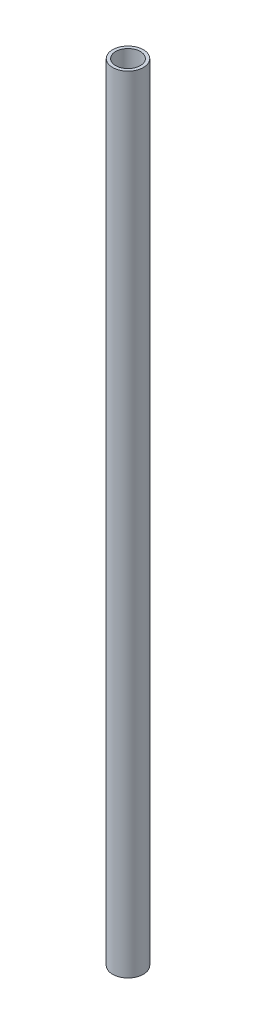
SolidWorks part; units mm, degrees
ref_plane "前视基准面" through (0, 0, 0) normal (0, 0, 1) x (1, 0, 0)
ref_plane "上视基准面" through (0, 0, 0) normal (0, 1, 0) x (1, 0, 0)
ref_plane "右视基准面" through (0, 0, 0) normal (1, 0, 0) x (0, 0, -1)
sketch "草图1" plane through (0, 0, 0) normal (0, 1, 0) x (1, 0, 0)
  circle A0 centre (0, 0) radius 10
  dimension "D1" = 20
extrude "凸台-拉伸1" add sketch "草图1" along normal blind 510
shell "抽壳1" thickness 2
